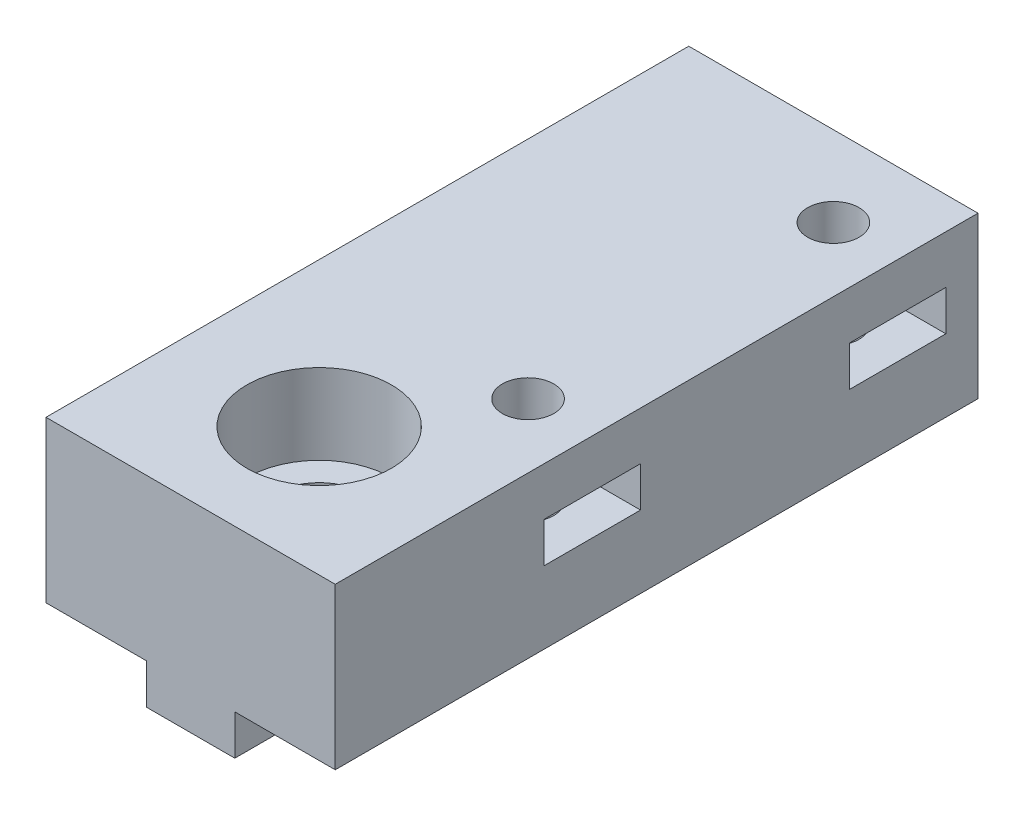
SolidWorks part; units mm, degrees
ref_plane "Front Plane" through (0, 0, 0) normal (0, 0, 1) x (1, 0, 0)
ref_plane "Top Plane" through (0, 0, 0) normal (0, 1, 0) x (1, 0, 0)
ref_plane "Right Plane" through (0, 0, 0) normal (1, 0, 0) x (0, 0, -1)
sketch "Sketch1" plane through (0, 0, 0) normal (0, 1, 0) x (1, 0, 0)
  line L1 (-0.6968, 0) -> (17.3032, 0)
  line L2 (-0.6968, 0) -> (-0.6968, 40)
  line L3 (-0.6968, 40) -> (17.3032, 40)
  line L4 (17.3032, 0) -> (17.3032, 40)
  dimension "D1" = 40
  dimension "D2" = 18
extrude "Boss-Extrude1" add sketch "Sketch1" along normal blind 10
sketch "Sketch3" plane through (0, 0, 0) normal (0, -1, 0) x (1, 0, 0)
  line L0 (-0.6968, -40) -> (-0.6968, 0) construction
  line L1 (17.3032, -40) -> (-0.6968, -40) construction
  line L2 (5.5532, -40) -> (11.0532, -40)
  line L3 (5.5532, -40) -> (5.5532, 0)
  line L4 (5.5532, 0) -> (11.0532, 0)
  line L7 (11.0532, -40) -> (11.0532, 0)
  dimension "D1" = 5.5
  dimension "D2" = 6.25
extrude "Boss-Extrude5" add sketch "Sketch3" along normal blind 2.5
sketch "Sketch2" plane through (0, 10, 0) normal (0, 1, 0) x (1, 0, 0)
  line L0 (17.3032, 40) -> (-0.6968, 40) construction
  line L1 (-0.6968, 40) -> (-0.6968, 0) construction
  circle A0 centre (8.3032, 8) radius 2.8
  dimension "D1" = 5.6
  dimension "D5" = 32
  dimension "D9" = 9
extrude "Cut-Extrude1" cut sketch "Sketch2" against normal through all
sketch "Sketch4" plane through (0, 10, 0) normal (0, 1, 0) x (1, 0, 0)
  circle A0 centre (8.3032, 8) radius 4.5
  dimension "D1" = 9
extrude "Cut-Extrude2" cut sketch "Sketch4" against normal blind 5
sketch "Sketch5" plane through (0, 10, 0) normal (0, 1, 0) x (1, 0, 0)
  line L0 (17.3032, 0) -> (17.3032, 40) construction
  line L1 (-0.6968, 0) -> (17.3032, 0) construction
  circle A0 centre (13.3032, 16) radius 1.6
  circle A1 centre (13.3032, 35) radius 1.6
  dimension "D1" = 3.2
  dimension "D2" = 3.2
  dimension "D3" = 4
  dimension "D4" = 4
  dimension "D5" = 19
  dimension "D6" = 16
extrude "Cut-Extrude3" cut sketch "Sketch5" against normal through all
sketch "Sketch6" plane through (17.3032, 0, 0) normal (1, 0, 0) x (0, 0, -1)
  line L0 (0, 10) -> (40, 10) construction
  line L1 (13, 7) -> (19, 7)
  line L2 (13, 7) -> (13, 4.5)
  line L3 (13, 4.5) -> (19, 4.5)
  line L4 (19, 7) -> (19, 4.5)
  line L5 (32, 7) -> (38, 7)
  line L6 (32, 7) -> (32, 4.5)
  line L7 (32, 4.5) -> (38, 4.5)
  line L8 (38, 7) -> (38, 4.5)
  line L9 (0, 10) -> (0, 0) construction
  dimension "D1" = 2.5
  dimension "D2" = 6
  dimension "D3" = 2.5
  dimension "D4" = 6
  dimension "D5" = 13
  dimension "D6" = 19
  dimension "D7" = 3
  dimension "D8" = 3
extrude "Cut-Extrude4" cut sketch "Sketch6" against normal blind 8
